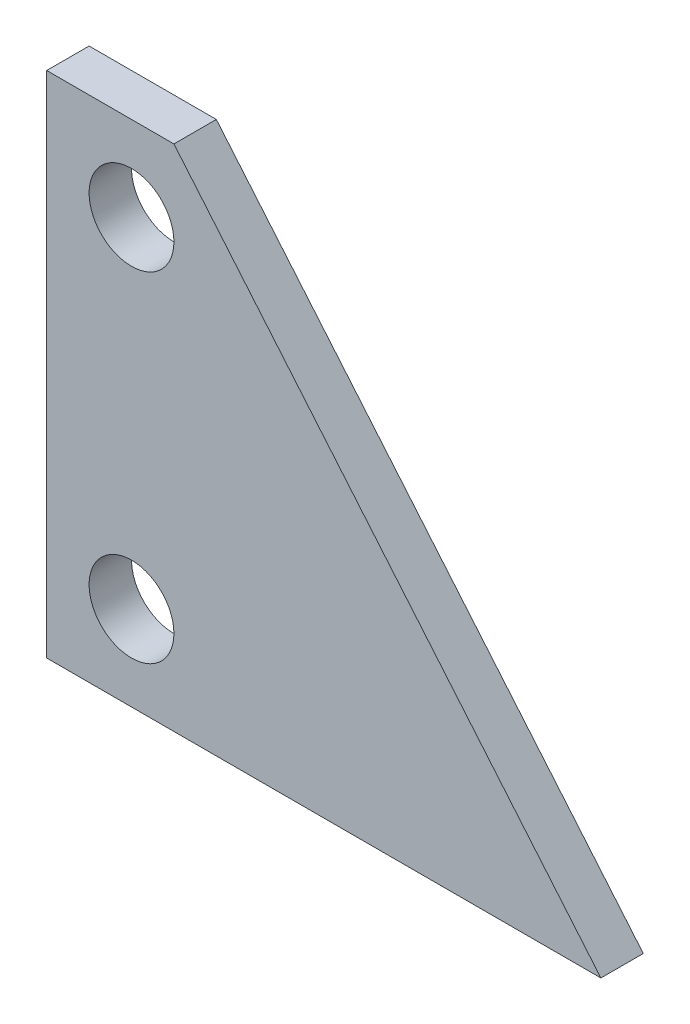
SolidWorks part; units mm, degrees
ref_plane "Front Plane" through (0, 0, 0) normal (0, 0, 1) x (1, 0, 0)
ref_plane "Top Plane" through (0, 0, 0) normal (0, 1, 0) x (1, 0, 0)
ref_plane "Right Plane" through (0, 0, 0) normal (1, 0, 0) x (0, 0, -1)
sketch "Sketch1" plane through (0, 0, 0) normal (0, 0, 1) x (1, 0, 0)
  line L0 (0, 0) -> (82.9894, 0)
  line L1 (82.9894, 0) -> (19.05, 76.2)
  line L2 (19.05, 76.2) -> (0, 76.2)
  line L3 (0, 76.2) -> (0, 0)
  line L4 (12.7, 76.2) -> (12.7, 0) construction
  circle A0 centre (12.7, 63.5) radius 6.35
  circle A1 centre (12.7, 12.7) radius 6.35
  point P11 (0, 0)
  point P12 (9.525, 63.3279)
  point P13 (0, 0)
  point P14 (9.525, 76.2)
  dimension "D4" = 12.7
  dimension "D1" = 12.7
  dimension "D2" = 50
  dimension "D3" = 76.2
  dimension "D5" = 12.7
  dimension "D6" = 12.7
  dimension "D7" = 19.05
extrude "Boss-Extrude1" add sketch "Sketch1" along normal mid plane 6.35
